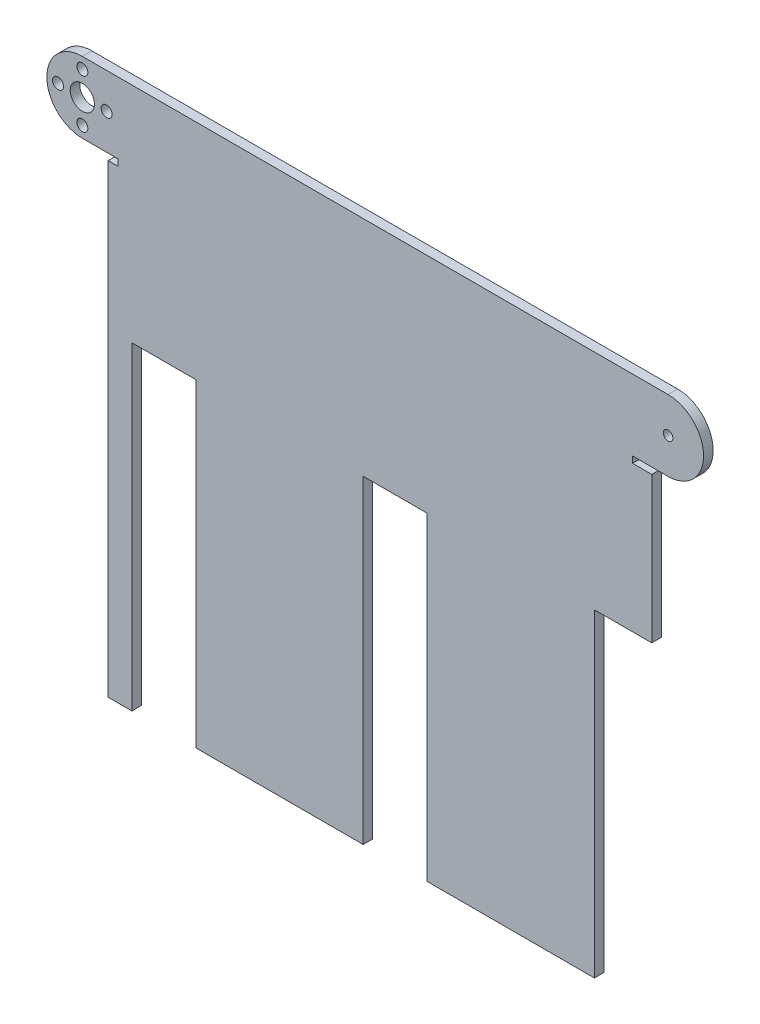
SolidWorks part; units mm, degrees
ref_plane "Plan de face" through (0, 0, 0) normal (0, 0, 1) x (1, 0, 0)
ref_plane "Plan de dessus" through (0, 0, 0) normal (0, 1, 0) x (1, 0, 0)
ref_plane "Plan de droite" through (0, 0, 0) normal (1, 0, 0) x (0, 0, -1)
sketch "Esquisse1" plane through (0, 0, 0) normal (0, 0, 1) x (1, 0, 0)
  line L0 (19.2104, -67.2251) -> (26.6604, -67.2251)
  line L1 (11.0904, 102.7749) -> (194.7804, 102.7749)
  line L2 (189.6604, 32.7749) -> (189.6604, 78.5349)
  line L3 (46.6604, -67.2251) -> (99.1604, -67.2251)
  line L4 (189.6604, 78.5349) -> (183.6604, 78.5349)
  line L5 (119.1604, -67.2251) -> (171.6604, -67.2251)
  line L6 (26.6604, -67.2251) -> (26.6604, 32.7749)
  line L7 (26.6604, 32.7749) -> (46.6604, 32.7749)
  line L8 (46.6604, -67.2251) -> (46.6604, 32.7749)
  line L9 (183.6604, 78.5349) -> (183.6604, 80.5349)
  line L10 (99.1604, -67.2251) -> (99.1604, 32.7749)
  line L11 (99.1604, 32.7749) -> (119.1604, 32.7749)
  line L12 (119.1604, -67.2251) -> (119.1604, 32.7749)
  line L13 (183.6604, 80.5349) -> (194.7804, 80.5349)
  line L14 (171.6604, -67.2251) -> (171.6604, 32.7749)
  line L15 (171.6604, 32.7749) -> (189.6604, 32.7749)
  line L16 (11.0904, 80.5349) -> (22.2104, 80.5349)
  line L17 (22.2104, 80.5349) -> (22.2104, 78.5349)
  line L18 (22.2104, 78.5349) -> (19.2104, 78.5349)
  line L19 (19.2104, 78.5349) -> (19.2104, -67.2251)
  arc A0 (194.7804, 80.5349) -> (194.7804, 102.7749) centre (194.7804, 91.6549) ccw
  arc A1 (11.0904, 102.7749) -> (11.0904, 80.5349) centre (11.0904, 91.6549) ccw
  circle A2 centre (194.7804, 91.6549) radius 1.5
  circle A3 centre (11.0904, 91.6549) radius 3.8
  circle A4 centre (11.0904, 99.2649) radius 1.725
  circle A5 centre (18.7004, 91.6549) radius 1.725
  circle A6 centre (11.0904, 84.0449) radius 1.725
  circle A7 centre (3.4804, 91.6549) radius 1.725
  dimension "D11" = 11.12
  dimension "D15" = 3
  dimension "D16" = 7.6
  dimension "D17" = 3.45
  dimension "D1" = 170
  dimension "D2" = 2
  dimension "D3" = 20
  dimension "D4" = 18
  dimension "D5" = 20
  dimension "D6" = 7.45
  dimension "D7" = 52.5
  dimension "D8" = 52.5
  dimension "D9" = 3
  dimension "D10" = 6
  dimension "D12" = 100
  dimension "D13" = 11.12
  dimension "D14" = 11.12
  dimension "D18" = 7.61
  dimension "D19" = 4
extrude "Boss.-Extru.1" add sketch "Esquisse1" along normal blind 3
